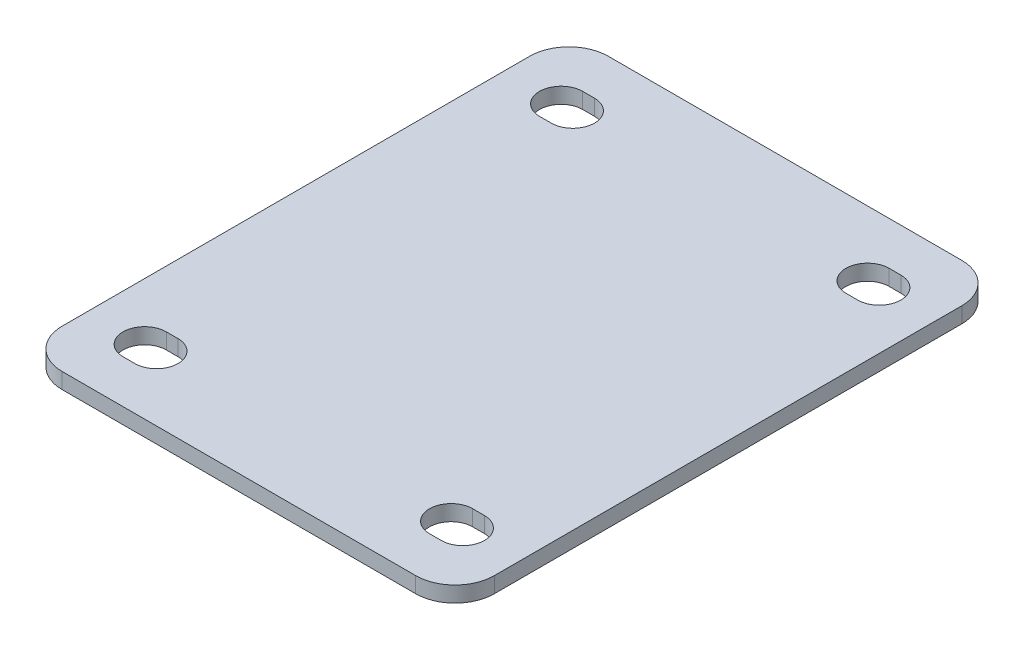
SolidWorks part; units mm, degrees
material "6063-T5"
ref_plane "Front Plane" through (0, 0, 0) normal (0, 0, 1) x (1, 0, 0)
ref_plane "Top Plane" through (0, 0, 0) normal (0, 1, 0) x (1, 0, 0)
ref_plane "Right Plane" through (0, 0, 0) normal (1, 0, 0) x (0, 0, -1)
sketch "Sketch1" plane through (0, 0, 0) normal (0, 1, 0) x (1, 0, 0)
  line L0 (-40.5, 53) -> (-37.5, 53) construction
  line L1 (-55, 69.5) -> (55, 69.5)
  line L2 (-55, 69.5) -> (-55, -69.5)
  line L3 (-55, -69.5) -> (55, -69.5)
  line L4 (55, 69.5) -> (55, -69.5)
  line L5 (-55, 69.5) -> (55, -69.5) construction
  line L6 (-55, -69.5) -> (55, 69.5) construction
  line L7 (-40.5, 58.5) -> (-37.5, 58.5)
  line L8 (-40.5, 47.5) -> (-37.5, 47.5)
  line L9 (37.5, 53) -> (40.5, 53) construction
  line L10 (37.5, 58.5) -> (40.5, 58.5)
  line L11 (37.5, 47.5) -> (40.5, 47.5)
  line L12 (-40.5, -53) -> (-37.5, -53) construction
  line L13 (-40.5, -47.5) -> (-37.5, -47.5)
  line L14 (-40.5, -58.5) -> (-37.5, -58.5)
  line L15 (37.5, -53) -> (40.5, -53) construction
  line L16 (37.5, -47.5) -> (40.5, -47.5)
  line L17 (37.5, -58.5) -> (40.5, -58.5)
  arc A0 (-40.5, 58.5) -> (-40.5, 47.5) centre (-40.5, 53) ccw
  arc A1 (-37.5, 47.5) -> (-37.5, 58.5) centre (-37.5, 53) ccw
  arc A2 (37.5, 58.5) -> (37.5, 47.5) centre (37.5, 53) ccw
  arc A3 (40.5, 47.5) -> (40.5, 58.5) centre (40.5, 53) ccw
  arc A4 (-40.5, -47.5) -> (-40.5, -58.5) centre (-40.5, -53) ccw
  arc A5 (-37.5, -58.5) -> (-37.5, -47.5) centre (-37.5, -53) ccw
  arc A6 (37.5, -47.5) -> (37.5, -58.5) centre (37.5, -53) ccw
  arc A7 (40.5, -58.5) -> (40.5, -47.5) centre (40.5, -53) ccw
  point P0 (0, 0)
  point P8 (-39, 53)
  point P13 (-46, 53)
  point P14 (-32, 53)
  point P15 (-39, 58.5)
  point P20 (39, 53)
  point P27 (-39, -53)
  point P34 (39, -53)
  dimension "D8" = 2
  dimension "D1" = 139
  dimension "D2" = 110
  dimension "D3" = 14
  dimension "D4" = 11
  dimension "D5" = 9
  dimension "D6" = 11
  dimension "D9" = 11
  dimension "D7" = 2
extrude "Boss-Extrude1" add sketch "Sketch1" along normal blind 4
fillet "Fillet1" radius 10 4 edges at (-55, 2, -69.5) (55, 2, -69.5) (55, 2, 69.5) (-55, 2, 69.5)
